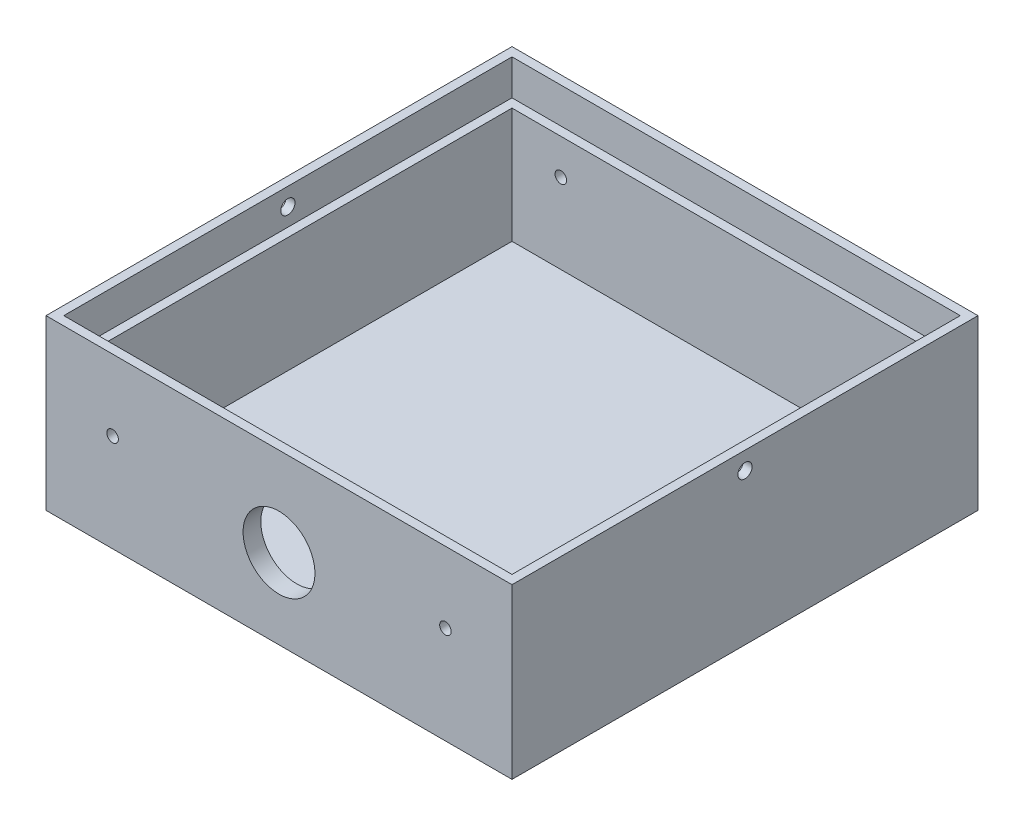
SolidWorks part; units mm, degrees
ref_plane "Front Plane" through (0, 0, 0) normal (0, 0, 1) x (1, 0, 0)
ref_plane "Top Plane" through (0, 0, 0) normal (0, 1, 0) x (1, 0, 0)
ref_plane "Right Plane" through (0, 0, 0) normal (1, 0, 0) x (0, 0, -1)
sketch "Sketch1" plane through (0, 0, 0) normal (0, 1, 0) x (1, 0, 0)
  line L1 (-52.5, 52.5) -> (52.5, 52.5)
  line L2 (-52.5, 52.5) -> (-52.5, -52.5)
  line L3 (-52.5, -52.5) -> (52.5, -52.5)
  line L4 (52.5, 52.5) -> (52.5, -52.5)
  line L5 (-52.5, 52.5) -> (52.5, -52.5) construction
  line L6 (-52.5, -52.5) -> (52.5, 52.5) construction
  point P0 (0, 0)
  dimension "D1" = 105
  dimension "D2" = 105
extrude "Boss-Extrude1" add sketch "Sketch1" along normal blind 38
sketch "Sketch2" plane through (0, 38, 0) normal (0, 1, 0) x (1, 0, 0)
  line L0 (-52.5, 52.5) -> (-52.5, -52.5) construction
  line L1 (-48.5, 48.5) -> (48.5, 48.5)
  line L2 (-48.5, 48.5) -> (-48.5, -48.5)
  line L3 (-48.5, -48.5) -> (48.5, -48.5)
  line L4 (48.5, 48.5) -> (48.5, -48.5)
  line L5 (-48.5, 48.5) -> (48.5, -48.5) construction
  line L6 (-48.5, -48.5) -> (48.5, 48.5) construction
  line L7 (52.5, 52.5) -> (-52.5, 52.5) construction
  point P0 (0, 0)
  dimension "D1" = 4
  dimension "D2" = 4
extrude "Cut-Extrude1" cut sketch "Sketch2" against normal blind 34
sketch "Sketch3" plane through (0, 38, 0) normal (0, 1, 0) x (1, 0, 0)
  line L0 (-52.5, 52.5) -> (-52.5, -52.5) construction
  line L1 (-50.5, 50.5) -> (50.5, 50.5)
  line L2 (-50.5, 50.5) -> (-50.5, -50.5)
  line L3 (-50.5, -50.5) -> (50.5, -50.5)
  line L4 (50.5, 50.5) -> (50.5, -50.5)
  line L5 (-50.5, 50.5) -> (50.5, -50.5) construction
  line L6 (-50.5, -50.5) -> (50.5, 50.5) construction
  line L7 (52.5, 52.5) -> (-52.5, 52.5) construction
  point P0 (0, 0)
  dimension "D1" = 2
  dimension "D2" = 2
extrude "Cut-Extrude2" cut sketch "Sketch3" against normal blind 8
sketch "Sketch5" plane through (52.5, 0, 0) normal (1, 0, 0) x (0, 0, -1)
  line L0 (-52.5, 38) -> (52.5, 38) construction
  circle A0 centre (0, 34) radius 1.6
  dimension "D1" = 3.2
  dimension "D2" = 4
extrude "Cut-Extrude3" cut sketch "Sketch5" against normal through all
sketch "Sketch6" plane through (0, 0, -52.5) normal (0, 0, -1) x (-1, 0, 0)
  line L0 (-52.5, 0) -> (52.5, 0) construction
  line L1 (-12, 0) -> (12, 0)
  line L2 (-12, 0) -> (-12, -5)
  line L4 (12, 0) -> (12, -5)
  line L5 (-52.5, 38) -> (-52.5, 0) construction
  line L8 (-12, -5) -> (-12, -17)
  line L10 (12, -5) -> (12, -17)
  arc A0 (-12, -17) -> (12, -17) centre (0, -17) ccw
  circle A1 centre (0, -17) radius 2.75
  dimension "D5" = 5.5
  dimension "D1" = 5
  dimension "D2" = 24
  dimension "D3" = 40.5
  dimension "D4" = 12
extrude "Boss-Extrude2" add sketch "Sketch6" against normal blind 3
fillet "Fillet1" radius 4 3 edges at (-12, 0, -51) (12, 0, -51) (0, 0, -49.5)
sketch "Sketch7" plane through (0, 0, 48.5) normal (0, 0, -1) x (-1, 0, 0)
  line L0 (-48.5, 30) -> (48.5, 30) construction
  circle A0 centre (0, 18) radius 8.1
  dimension "D1" = 16.2
  dimension "D2" = 12
extrude "Cut-Extrude4" cut sketch "Sketch7" against normal up to next
sketch "Sketch10" plane through (0, 0, 0) normal (0, -1, 0) x (1, 0, 0)
  line L1 (5, -10) -> (0, -10)
  line L2 (5, -10) -> (5, 10)
  line L3 (5, 10) -> (0, 10)
  line L5 (0, -7) -> (2, -7)
  line L7 (0, -3) -> (2, -3)
  line L8 (2, -7) -> (2, -3)
  line L9 (0, 3) -> (2, 3)
  line L11 (0, 7) -> (2, 7)
  line L12 (2, 3) -> (2, 7)
  arc A0 (0, 0) -> (0, -10) centre (0, -5) ccw
  arc A1 (0, 10) -> (0, 0) centre (0, 5) ccw
  arc A2 (0, -3) -> (0, -7) centre (0, -5) ccw
  arc A3 (0, 7) -> (0, 3) centre (0, 5) ccw
  dimension "D3" = 10
  dimension "D4" = 10
  dimension "D5" = 4
  dimension "D6" = 4
  dimension "D1" = 5
  dimension "D2" = 20
  dimension "D7" = 4
  dimension "D8" = 2
  dimension "D9" = 2
  dimension "D10" = 4
extrude "Cut-Extrude5" cut sketch "Sketch10" against normal blind 1
sketch "Sketch11" plane through (0, 0, 52.5) normal (0, 0, 1) x (1, 0, 0)
  line L0 (-52.5, 38) -> (-52.5, 0) construction
  line L1 (-52.5, 38) -> (52.5, 38) construction
  line L2 (0, 7.5861) -> (0, 33.6351) construction
  circle A0 centre (-37.5, 22) radius 1.3
  circle A1 centre (37.5, 22) radius 1.3
  dimension "D1" = 2.6
  dimension "D2" = 15
  dimension "D3" = 16
extrude "Cut-Extrude6" cut sketch "Sketch11" against normal through all
